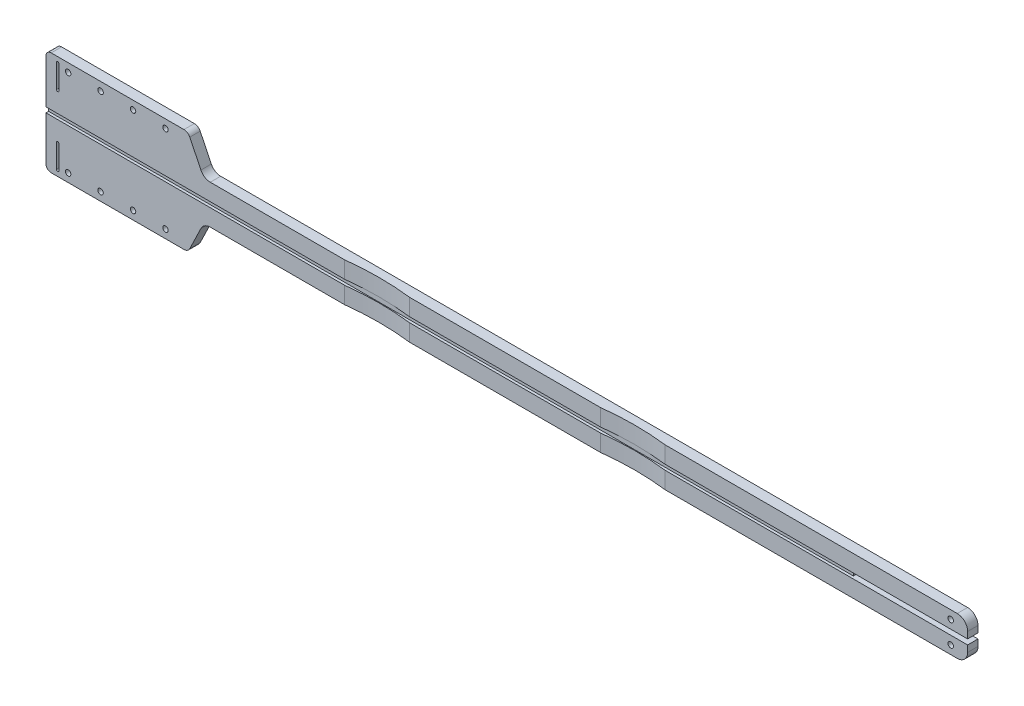
SolidWorks part; units mm, degrees
ref_plane "Plan de face" through (0, 0, 0) normal (0, 0, 1) x (1, 0, 0)
ref_plane "Plan de dessus" through (0, 0, 0) normal (0, 1, 0) x (1, 0, 0)
ref_plane "Plan de droite" through (0, 0, 0) normal (1, 0, 0) x (0, 0, -1)
sketch "Model" plane through (0, 0, 0) normal (0, 0, 1) x (1, 0, 0)
  line L0 (5.8076, 84.65) -> (5.8076, 156.65)
  line L1 (15.8076, 84.988) -> (15.8076, 102.988)
  line L2 (15.8076, 156.312) -> (15.8076, 138.312)
  line L3 (13.8076, 84.988) -> (13.8076, 102.988)
  line L4 (13.8076, 156.312) -> (13.8076, 138.312)
  line L5 (9.8076, 80.65) -> (112.09, 80.65)
  line L6 (9.8076, 160.65) -> (112.09, 160.65)
  line L7 (116.5907, 157.828) -> (125.1445, 140.152)
  line L8 (116.5907, 83.472) -> (125.1445, 101.148)
  line L9 (715.7592, 127.6368) -> (715.7592, 122.65)
  line L10 (715.7592, 113.6632) -> (715.7592, 118.65)
  line L11 (625.7592, 122.65) -> (625.7592, 118.65)
  line L12 (132.3456, 135.6368) -> (707.7592, 135.6368)
  line L13 (132.3456, 105.6632) -> (707.7592, 105.6632)
  line L14 (625.7592, 122.65) -> (715.7592, 122.65)
  line L15 (715.7592, 118.65) -> (625.7592, 118.65)
  circle A0 centre (702.7592, 129.1434) radius 2.1
  circle A1 centre (702.7592, 112.1566) radius 2.1
  circle A2 centre (47.8534, 154.15) radius 2.1
  circle A3 centre (97.8534, 154.15) radius 2.1
  circle A4 centre (22.8534, 154.15) radius 2.1
  circle A5 centre (72.8534, 154.15) radius 2.1
  circle A6 centre (47.8534, 87.15) radius 2.1
  circle A7 centre (97.8534, 87.15) radius 2.1
  circle A8 centre (22.8534, 87.15) radius 2.1
  circle A9 centre (72.8534, 87.15) radius 2.1
  arc A10 (112.09, 80.65) -> (116.5907, 83.472) centre (112.09, 85.65) ccw
  arc A11 (116.5907, 157.828) -> (112.09, 160.65) centre (112.09, 155.65) ccw
  arc A12 (5.8076, 84.65) -> (9.8076, 80.65) centre (9.8076, 84.65) ccw
  arc A13 (9.8076, 160.65) -> (5.8076, 156.65) centre (9.8076, 156.65) ccw
  arc A14 (15.8076, 156.312) -> (13.8076, 156.312) centre (14.8076, 156.312) ccw
  arc A15 (13.8076, 138.312) -> (15.8076, 138.312) centre (14.8076, 138.312) ccw
  arc A16 (15.8076, 102.988) -> (13.8076, 102.988) centre (14.8076, 102.988) ccw
  arc A17 (13.8076, 84.988) -> (15.8076, 84.988) centre (14.8076, 84.988) ccw
  arc A18 (125.1445, 140.152) -> (132.3456, 135.6368) centre (132.3456, 143.6368) ccw
  arc A19 (132.3456, 105.6632) -> (125.1445, 101.148) centre (132.3456, 97.6632) ccw
  arc A20 (715.7592, 127.6368) -> (707.7592, 135.6368) centre (707.7592, 127.6368) ccw
  arc A21 (707.7592, 105.6632) -> (715.7592, 113.6632) centre (707.7592, 113.6632) ccw
extrude "Boss.-Extru.1" add sketch "Model" along normal blind 8
sketch "Esquisse2" plane through (0, 0, 8) normal (0, 0, 1) x (1, 0, 0)
  line L0 (625.7592, 122.65) -> (5.8076, 122.65)
  line L1 (5.8076, 156.65) -> (5.8076, 84.65) construction
  line L2 (625.7592, 122.65) -> (625.7592, 118.65)
  line L3 (625.7592, 118.65) -> (5.8076, 118.65)
  line L4 (5.8076, 118.65) -> (5.8076, 122.65)
extrude "Enlèv. mat.-Extru.1" cut sketch "Esquisse2" against normal blind 2
chamfer "Chanfrein1" distance 1 angle 45 18 edges at (704.8592, 112.1566, 0) (704.8592, 129.1434, 0) (15.8076, 93.988, 0) (14.8076, 103.988, 0) (14.8076, 83.988, 0) (13.8076, 93.988, 0) (99.9534, 87.15, 0) (74.9534, 87.15, 0) (49.9534, 87.15, 0) (24.9534, 87.15, 0) (99.9534, 154.15, 0) (74.9534, 154.15, 0) (49.9534, 154.15, 0) (24.9534, 154.15, 0) (15.8076, 147.312, 0) (14.8076, 157.312, 0) (14.8076, 137.312, 0) (13.8076, 147.312, 0)
sketch "Esquisse3" plane through (0, 105.6632, 0) normal (0, -1, 0) x (1, 0, 0)
  line L0 (235.8076, 8) -> (285.8076, 8)
  line L1 (132.3456, 8) -> (707.7592, 8) construction
  line L2 (432.8076, 8) -> (482.8076, 8)
  arc A0 (235.8076, 8) -> (285.8076, 8) centre (260.8076, 215.5833) ccw
  arc A1 (432.8076, 8) -> (482.8076, 8) centre (457.8076, 215.5833) ccw
  point P8 (260.8076, 6.5)
  point P10 (457.8076, 6.5)
  dimension "D1" = 230
  dimension "D2" = 50
  dimension "D3" = 427
  dimension "D4" = 50
  dimension "D5" = 1.5
  dimension "D6" = 1.5
extrude "Enlèv. mat.-Extru.2" cut sketch "Esquisse3" against normal through all
